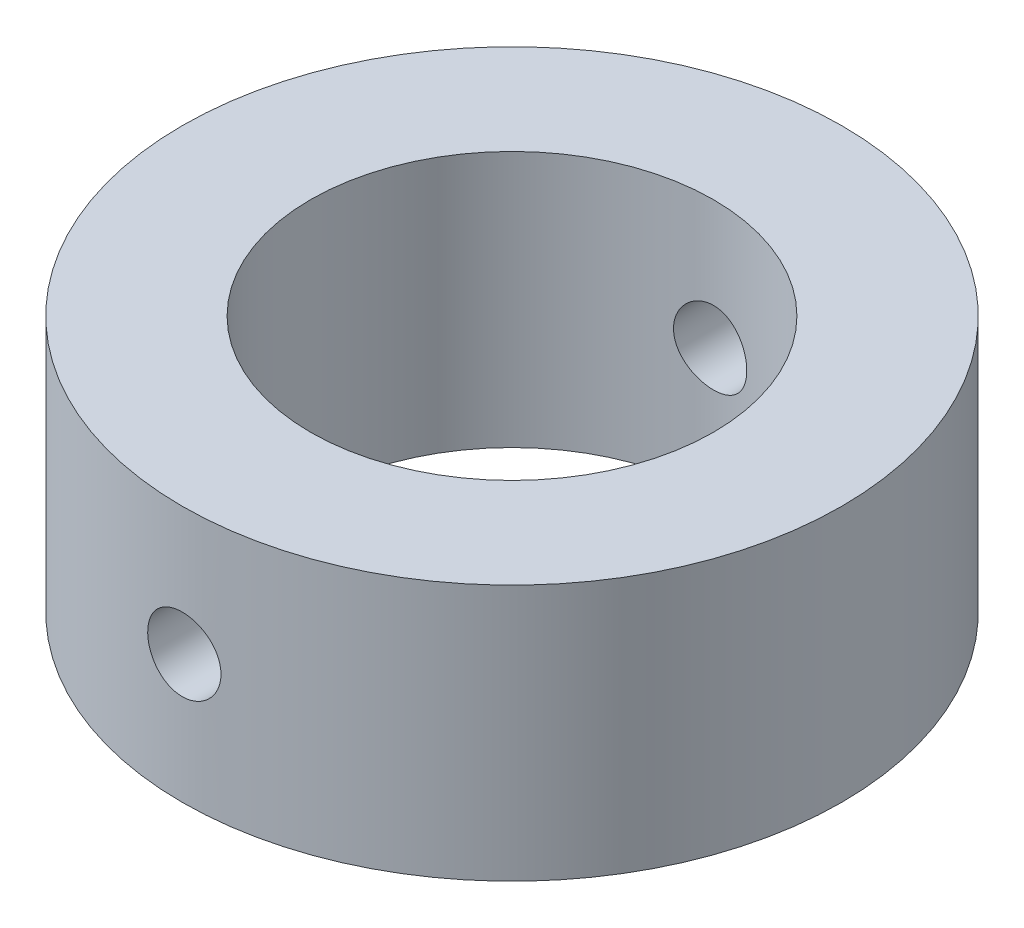
SolidWorks part; units mm, degrees
ref_plane "Front Plane" through (0, 0, 0) normal (0, 0, 1) x (1, 0, 0)
ref_plane "Top Plane" through (0, 0, 0) normal (0, 1, 0) x (1, 0, 0)
ref_plane "Right Plane" through (0, 0, 0) normal (1, 0, 0) x (0, 0, -1)
sketch "Sketch1" plane through (0, 0, 0) normal (0, 1, 0) x (1, 0, 0)
  circle A0 centre (0, 0) radius 18
  circle A1 centre (0, 0) radius 11
  dimension "D1" = 22
  dimension "D2" = 36
extrude "Boss-Extrude1" add sketch "Sketch1" along normal mid plane 14
sketch "Sketch2" plane through (0, 0, 0) normal (0, 0, 1) x (1, 0, 0)
  circle A0 centre (0, 0) radius 2
  dimension "D1" = 4
extrude "Cut-Extrude1" cut sketch "Sketch2" against normal through all both and the other way through all
